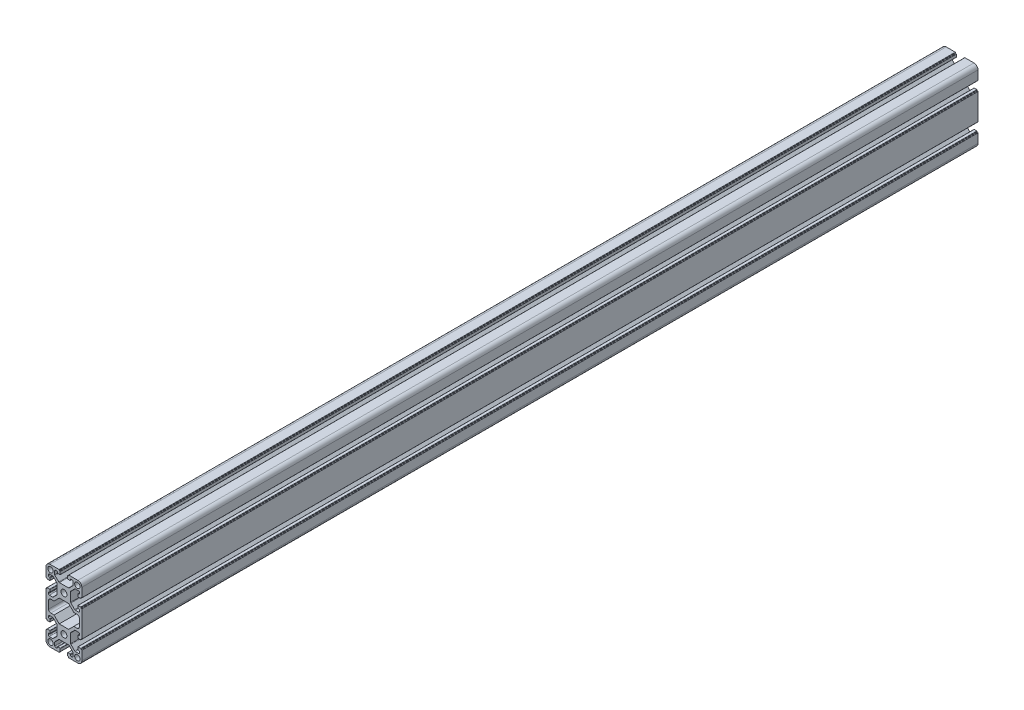
SolidWorks part; units mm, degrees
material "6063 T5"
ref_plane "Спереди" through (0, 0, 0) normal (0, 0, 1) x (1, 0, 0)
ref_plane "Сверху" through (0, 0, 0) normal (0, 1, 0) x (1, 0, 0)
ref_plane "Справа" through (0, 0, 0) normal (1, 0, 0) x (0, 0, -1)
sketch "Эскиз1" plane through (0, 0, 0) normal (0, 0, 1) x (1, 0, 0)
  line L0 (-19.98, 20.5457) -> (20.02, 20.5457) construction
  line L1 (-20, 10.25) -> (-20, 15.5)
  line L2 (-15.5, 20) -> (-10.25, 20)
  line L3 (10.25, 20) -> (15.5, 20)
  line L8 (20, 15.5) -> (20, 10.25)
  line L13 (0, 0) -> (0, -40) construction
  line L14 (0, -20) -> (-27.0056, -20) construction
  line L19 (20, -55.5) -> (20, -50.25)
  line L20 (10.25, -60) -> (15.5, -60)
  line L25 (-15.5, -60) -> (-10.25, -60)
  line L26 (-20.0124, 26.0326) -> (19.9876, 26.0326) construction
  line L27 (-20, -50.25) -> (-20, -55.5)
  line L28 (-20, -10.25) -> (-20, -29.75)
  line L29 (20, -10.25) -> (20, -29.75)
  line L30 (-17.2, -24.25) -> (-17.2, -15.75)
  line L31 (-14.7, -13.25) -> (-11.0074, -13.25)
  line L32 (-11.0074, -13.25) -> (-5.2574, -7.5)
  line L33 (-5.2574, -7.5) -> (5.2574, -7.5)
  line L34 (-29.9759, 20.027) -> (-29.9759, -59.973) construction
  line L35 (11.0074, -13.25) -> (5.2574, -7.5)
  line L36 (14.7, -13.25) -> (11.0074, -13.25)
  line L37 (17.2, -24.25) -> (17.2, -15.75)
  line L38 (-14.7, -26.75) -> (-11.0074, -26.75)
  line L39 (-11.0074, -26.75) -> (-5.2574, -32.5)
  line L40 (-5.2574, -32.5) -> (5.2574, -32.5)
  line L41 (11.0074, -26.75) -> (5.2574, -32.5)
  line L42 (14.7, -26.75) -> (11.0074, -26.75)
  line L45 (20, -10.25) -> (20, -15.5) [skipped]
  line L46 (15.5, -20) -> (10.25, -20) [skipped]
  line L47 (-10.25, -20) -> (-15.5, -20) [skipped]
  line L48 (-20, -15.5) -> (-20, -10.25) [skipped]
  arc A0 (-20, 15.5) -> (-15.5, 20) centre (-15.5, 15.5) cw
  circle A5 centre (0, 0) radius 3.35
  arc A6 (15.5, 20) -> (20, 15.5) centre (15.5, 15.5) cw
  circle A11 centre (15, 15) radius 3
  circle A16 centre (-15, -55) radius 3
  circle A21 centre (15, -55) radius 3
  arc A22 (15.5, -60) -> (20, -55.5) centre (15.5, -55.5) ccw
  circle A23 centre (0, -40) radius 3.35
  arc A24 (-20, -55.5) -> (-15.5, -60) centre (-15.5, -55.5) ccw
  arc A25 (-17.2, -15.75) -> (-14.7, -13.25) centre (-14.7, -15.75) cw
  arc A26 (17.2, -15.75) -> (14.7, -13.25) centre (14.7, -15.75) ccw
  arc A27 (-17.2, -24.25) -> (-14.7, -26.75) centre (-14.7, -24.25) ccw
  arc A28 (17.2, -24.25) -> (14.7, -26.75) centre (14.7, -24.25) cw
  circle A33 centre (-15, 15) radius 3
  arc A37 (20, -15.5) -> (15.5, -20) centre (15.5, -15.5) cw [skipped]
  circle A38 centre (15, -15) radius 3 [skipped]
  arc A39 (-15.5, -20) -> (-20, -15.5) centre (-15.5, -15.5) cw [skipped]
  circle A40 centre (-15, -15) radius 3 [skipped]
  point P5 (0, 0)
  point P35 (0, -40)
  point P36 (0, -40)
  point P38 (0, 0)
  point P63 (0, -7.5)
  point P71 (-17.2, -20)
  point P75 (17.2, -20)
  line B0 (-20, 10.25) -> (-20, 5.4)
  line B1 (-19.7, 5.1) -> (-19.3, 5.1)
  line B2 (-19, 4.8) -> (-19, 4.4)
  line B3 (-18.7, 4.1) -> (-15.8, 4.1)
  line B4 (-15.5, 4.4) -> (-15.5, 6.8)
  line B5 (-15.8, 7.1) -> (-16.3, 7.1)
  line B6 (-17.3, 8.1) -> (-17.3, 9.25)
  line B7 (-16.3, 10.25) -> (-12.6642, 10.25)
  line B8 (-11.9571, 9.9571) -> (-7.7929, 5.7929)
  line B9 (-7.5, 5.0858) -> (-7.5, -5.0858)
  line B10 (-7.5, 0) -> (-20, 0) construction
  line B11 (-11.9571, -9.9571) -> (-7.7929, -5.7929)
  line B12 (-16.3, -10.25) -> (-12.6642, -10.25)
  line B13 (-17.3, -8.1) -> (-17.3, -9.25)
  line B14 (-15.8, -7.1) -> (-16.3, -7.1)
  line B15 (-15.5, -4.4) -> (-15.5, -6.8)
  line B16 (-18.7, -4.1) -> (-15.8, -4.1)
  line B17 (-19, -4.8) -> (-19, -4.4)
  line B18 (-19.7, -5.1) -> (-19.3, -5.1)
  line B19 (-20, -10.25) -> (-20, -5.4)
  arc B20 (-15.5, 6.8) -> (-15.8, 7.1) centre (-15.8, 6.8) ccw
  arc B21 (-15.8, 4.1) -> (-15.5, 4.4) centre (-15.8, 4.4) ccw
  arc B22 (-19, 4.4) -> (-18.7, 4.1) centre (-18.7, 4.4) ccw
  arc B23 (-19.3, 5.1) -> (-19, 4.8) centre (-19.3, 4.8) cw
  arc B24 (-20, 5.4) -> (-19.7, 5.1) centre (-19.7, 5.4) ccw
  arc B25 (-7.7929, 5.7929) -> (-7.5, 5.0858) centre (-8.5, 5.0858) cw
  arc B26 (-12.6642, 10.25) -> (-11.9571, 9.9571) centre (-12.6642, 9.25) cw
  arc B27 (-17.3, 9.25) -> (-16.3, 10.25) centre (-16.3, 9.25) cw
  arc B28 (-16.3, 7.1) -> (-17.3, 8.1) centre (-16.3, 8.1) cw
  arc B29 (-16.3, -7.1) -> (-17.3, -8.1) centre (-16.3, -8.1) ccw
  arc B30 (-17.3, -9.25) -> (-16.3, -10.25) centre (-16.3, -9.25) ccw
  arc B31 (-12.6642, -10.25) -> (-11.9571, -9.9571) centre (-12.6642, -9.25) ccw
  arc B32 (-7.7929, -5.7929) -> (-7.5, -5.0858) centre (-8.5, -5.0858) ccw
  arc B33 (-20, -5.4) -> (-19.7, -5.1) centre (-19.7, -5.4) cw
  arc B34 (-19.3, -5.1) -> (-19, -4.8) centre (-19.3, -4.8) ccw
  arc B35 (-19, -4.4) -> (-18.7, -4.1) centre (-18.7, -4.4) cw
  arc B36 (-15.8, -4.1) -> (-15.5, -4.4) centre (-15.8, -4.4) cw
  arc B37 (-15.5, -6.8) -> (-15.8, -7.1) centre (-15.8, -6.8) cw
  line B38 (10.25, 20) -> (5.4, 20)
  line B39 (5.1, 19.7) -> (5.1, 19.3)
  line B40 (4.8, 19) -> (4.4, 19)
  line B41 (4.1, 18.7) -> (4.1, 15.8)
  line B42 (4.4, 15.5) -> (6.8, 15.5)
  line B43 (7.1, 15.8) -> (7.1, 16.3)
  line B44 (8.1, 17.3) -> (9.25, 17.3)
  line B45 (10.25, 16.3) -> (10.25, 12.6642)
  line B46 (9.9571, 11.9571) -> (5.7929, 7.7929)
  line B47 (5.0858, 7.5) -> (-5.0858, 7.5)
  line B48 (0, 7.5) -> (0, 20) construction
  line B49 (-9.9571, 11.9571) -> (-5.7929, 7.7929)
  line B50 (-10.25, 16.3) -> (-10.25, 12.6642)
  line B51 (-8.1, 17.3) -> (-9.25, 17.3)
  line B52 (-7.1, 15.8) -> (-7.1, 16.3)
  line B53 (-4.4, 15.5) -> (-6.8, 15.5)
  line B54 (-4.1, 18.7) -> (-4.1, 15.8)
  line B55 (-4.8, 19) -> (-4.4, 19)
  line B56 (-5.1, 19.7) -> (-5.1, 19.3)
  line B57 (-10.25, 20) -> (-5.4, 20)
  arc B58 (6.8, 15.5) -> (7.1, 15.8) centre (6.8, 15.8) ccw
  arc B59 (4.1, 15.8) -> (4.4, 15.5) centre (4.4, 15.8) ccw
  arc B60 (4.4, 19) -> (4.1, 18.7) centre (4.4, 18.7) ccw
  arc B61 (5.1, 19.3) -> (4.8, 19) centre (4.8, 19.3) cw
  arc B62 (5.4, 20) -> (5.1, 19.7) centre (5.4, 19.7) ccw
  arc B63 (5.7929, 7.7929) -> (5.0858, 7.5) centre (5.0858, 8.5) cw
  arc B64 (10.25, 12.6642) -> (9.9571, 11.9571) centre (9.25, 12.6642) cw
  arc B65 (9.25, 17.3) -> (10.25, 16.3) centre (9.25, 16.3) cw
  arc B66 (7.1, 16.3) -> (8.1, 17.3) centre (8.1, 16.3) cw
  arc B67 (-7.1, 16.3) -> (-8.1, 17.3) centre (-8.1, 16.3) ccw
  arc B68 (-9.25, 17.3) -> (-10.25, 16.3) centre (-9.25, 16.3) ccw
  arc B69 (-10.25, 12.6642) -> (-9.9571, 11.9571) centre (-9.25, 12.6642) ccw
  arc B70 (-5.7929, 7.7929) -> (-5.0858, 7.5) centre (-5.0858, 8.5) ccw
  arc B71 (-5.4, 20) -> (-5.1, 19.7) centre (-5.4, 19.7) cw
  arc B72 (-5.1, 19.3) -> (-4.8, 19) centre (-4.8, 19.3) ccw
  arc B73 (-4.4, 19) -> (-4.1, 18.7) centre (-4.4, 18.7) cw
  arc B74 (-4.1, 15.8) -> (-4.4, 15.5) centre (-4.4, 15.8) cw
  arc B75 (-6.8, 15.5) -> (-7.1, 15.8) centre (-6.8, 15.8) cw
  line B76 (20, -10.25) -> (20, -5.4)
  line B77 (19.7, -5.1) -> (19.3, -5.1)
  line B78 (19, -4.8) -> (19, -4.4)
  line B79 (18.7, -4.1) -> (15.8, -4.1)
  line B80 (15.5, -4.4) -> (15.5, -6.8)
  line B81 (15.8, -7.1) -> (16.3, -7.1)
  line B82 (17.3, -8.1) -> (17.3, -9.25)
  line B83 (16.3, -10.25) -> (12.6642, -10.25)
  line B84 (11.9571, -9.9571) -> (7.7929, -5.7929)
  line B85 (7.5, -5.0858) -> (7.5, 5.0858)
  line B86 (7.5, 0) -> (20, 0) construction
  line B87 (11.9571, 9.9571) -> (7.7929, 5.7929)
  line B88 (16.3, 10.25) -> (12.6642, 10.25)
  line B89 (17.3, 8.1) -> (17.3, 9.25)
  line B90 (15.8, 7.1) -> (16.3, 7.1)
  line B91 (15.5, 4.4) -> (15.5, 6.8)
  line B92 (18.7, 4.1) -> (15.8, 4.1)
  line B93 (19, 4.8) -> (19, 4.4)
  line B94 (19.7, 5.1) -> (19.3, 5.1)
  line B95 (20, 10.25) -> (20, 5.4)
  arc B96 (15.5, -6.8) -> (15.8, -7.1) centre (15.8, -6.8) ccw
  arc B97 (15.8, -4.1) -> (15.5, -4.4) centre (15.8, -4.4) ccw
  arc B98 (19, -4.4) -> (18.7, -4.1) centre (18.7, -4.4) ccw
  arc B99 (19.3, -5.1) -> (19, -4.8) centre (19.3, -4.8) cw
  arc B100 (20, -5.4) -> (19.7, -5.1) centre (19.7, -5.4) ccw
  arc B101 (7.7929, -5.7929) -> (7.5, -5.0858) centre (8.5, -5.0858) cw
  arc B102 (12.6642, -10.25) -> (11.9571, -9.9571) centre (12.6642, -9.25) cw
  arc B103 (17.3, -9.25) -> (16.3, -10.25) centre (16.3, -9.25) cw
  arc B104 (16.3, -7.1) -> (17.3, -8.1) centre (16.3, -8.1) cw
  arc B105 (16.3, 7.1) -> (17.3, 8.1) centre (16.3, 8.1) ccw
  arc B106 (17.3, 9.25) -> (16.3, 10.25) centre (16.3, 9.25) ccw
  arc B107 (12.6642, 10.25) -> (11.9571, 9.9571) centre (12.6642, 9.25) ccw
  arc B108 (7.7929, 5.7929) -> (7.5, 5.0858) centre (8.5, 5.0858) ccw
  arc B109 (20, 5.4) -> (19.7, 5.1) centre (19.7, 5.4) cw
  arc B110 (19.3, 5.1) -> (19, 4.8) centre (19.3, 4.8) ccw
  arc B111 (19, 4.4) -> (18.7, 4.1) centre (18.7, 4.4) cw
  arc B112 (15.8, 4.1) -> (15.5, 4.4) centre (15.8, 4.4) cw
  arc B113 (15.5, 6.8) -> (15.8, 7.1) centre (15.8, 6.8) cw
  line B114 (10.25, -60) -> (5.4, -60)
  line B115 (5.1, -59.7) -> (5.1, -59.3)
  line B116 (4.8, -59) -> (4.4, -59)
  line B117 (4.1, -58.7) -> (4.1, -55.8)
  line B118 (4.4, -55.5) -> (6.8, -55.5)
  line B119 (7.1, -55.8) -> (7.1, -56.3)
  line B120 (8.1, -57.3) -> (9.25, -57.3)
  line B121 (10.25, -56.3) -> (10.25, -52.6642)
  line B122 (9.9571, -51.9571) -> (5.7929, -47.7929)
  line B123 (5.0858, -47.5) -> (-5.0858, -47.5)
  line B124 (0, -47.5) -> (0, -60) construction
  line B125 (-9.9571, -51.9571) -> (-5.7929, -47.7929)
  line B126 (-10.25, -56.3) -> (-10.25, -52.6642)
  line B127 (-8.1, -57.3) -> (-9.25, -57.3)
  line B128 (-7.1, -55.8) -> (-7.1, -56.3)
  line B129 (-4.4, -55.5) -> (-6.8, -55.5)
  line B130 (-4.1, -58.7) -> (-4.1, -55.8)
  line B131 (-4.8, -59) -> (-4.4, -59)
  line B132 (-5.1, -59.7) -> (-5.1, -59.3)
  line B133 (-10.25, -60) -> (-5.4, -60)
  arc B134 (6.8, -55.5) -> (7.1, -55.8) centre (6.8, -55.8) cw
  arc B135 (4.1, -55.8) -> (4.4, -55.5) centre (4.4, -55.8) cw
  arc B136 (4.4, -59) -> (4.1, -58.7) centre (4.4, -58.7) cw
  arc B137 (5.1, -59.3) -> (4.8, -59) centre (4.8, -59.3) ccw
  arc B138 (5.4, -60) -> (5.1, -59.7) centre (5.4, -59.7) cw
  arc B139 (5.7929, -47.7929) -> (5.0858, -47.5) centre (5.0858, -48.5) ccw
  arc B140 (10.25, -52.6642) -> (9.9571, -51.9571) centre (9.25, -52.6642) ccw
  arc B141 (9.25, -57.3) -> (10.25, -56.3) centre (9.25, -56.3) ccw
  arc B142 (7.1, -56.3) -> (8.1, -57.3) centre (8.1, -56.3) ccw
  arc B143 (-7.1, -56.3) -> (-8.1, -57.3) centre (-8.1, -56.3) cw
  arc B144 (-9.25, -57.3) -> (-10.25, -56.3) centre (-9.25, -56.3) cw
  arc B145 (-10.25, -52.6642) -> (-9.9571, -51.9571) centre (-9.25, -52.6642) cw
  arc B146 (-5.7929, -47.7929) -> (-5.0858, -47.5) centre (-5.0858, -48.5) cw
  arc B147 (-5.4, -60) -> (-5.1, -59.7) centre (-5.4, -59.7) ccw
  arc B148 (-5.1, -59.3) -> (-4.8, -59) centre (-4.8, -59.3) cw
  arc B149 (-4.4, -59) -> (-4.1, -58.7) centre (-4.4, -58.7) ccw
  arc B150 (-4.1, -55.8) -> (-4.4, -55.5) centre (-4.4, -55.8) ccw
  arc B151 (-6.8, -55.5) -> (-7.1, -55.8) centre (-6.8, -55.8) ccw
  line B152 (-20, -50.25) -> (-20, -45.4)
  line B153 (-19.7, -45.1) -> (-19.3, -45.1)
  line B154 (-19, -44.8) -> (-19, -44.4)
  line B155 (-18.7, -44.1) -> (-15.8, -44.1)
  line B156 (-15.5, -44.4) -> (-15.5, -46.8)
  line B157 (-15.8, -47.1) -> (-16.3, -47.1)
  line B158 (-17.3, -48.1) -> (-17.3, -49.25)
  line B159 (-16.3, -50.25) -> (-12.6642, -50.25)
  line B160 (-11.9571, -49.9571) -> (-7.7929, -45.7929)
  line B161 (-7.5, -45.0858) -> (-7.5, -34.9142)
  line B162 (-7.5, -40) -> (-20, -40) construction
  line B163 (-11.9571, -30.0429) -> (-7.7929, -34.2071)
  line B164 (-16.3, -29.75) -> (-12.6642, -29.75)
  line B165 (-17.3, -31.9) -> (-17.3, -30.75)
  line B166 (-15.8, -32.9) -> (-16.3, -32.9)
  line B167 (-15.5, -35.6) -> (-15.5, -33.2)
  line B168 (-18.7, -35.9) -> (-15.8, -35.9)
  line B169 (-19, -35.2) -> (-19, -35.6)
  line B170 (-19.7, -34.9) -> (-19.3, -34.9)
  line B171 (-20, -29.75) -> (-20, -34.6)
  arc B172 (-15.5, -46.8) -> (-15.8, -47.1) centre (-15.8, -46.8) cw
  arc B173 (-15.8, -44.1) -> (-15.5, -44.4) centre (-15.8, -44.4) cw
  arc B174 (-19, -44.4) -> (-18.7, -44.1) centre (-18.7, -44.4) cw
  arc B175 (-19.3, -45.1) -> (-19, -44.8) centre (-19.3, -44.8) ccw
  arc B176 (-20, -45.4) -> (-19.7, -45.1) centre (-19.7, -45.4) cw
  arc B177 (-7.7929, -45.7929) -> (-7.5, -45.0858) centre (-8.5, -45.0858) ccw
  arc B178 (-12.6642, -50.25) -> (-11.9571, -49.9571) centre (-12.6642, -49.25) ccw
  arc B179 (-17.3, -49.25) -> (-16.3, -50.25) centre (-16.3, -49.25) ccw
  arc B180 (-16.3, -47.1) -> (-17.3, -48.1) centre (-16.3, -48.1) ccw
  arc B181 (-16.3, -32.9) -> (-17.3, -31.9) centre (-16.3, -31.9) cw
  arc B182 (-17.3, -30.75) -> (-16.3, -29.75) centre (-16.3, -30.75) cw
  arc B183 (-12.6642, -29.75) -> (-11.9571, -30.0429) centre (-12.6642, -30.75) cw
  arc B184 (-7.7929, -34.2071) -> (-7.5, -34.9142) centre (-8.5, -34.9142) cw
  arc B185 (-20, -34.6) -> (-19.7, -34.9) centre (-19.7, -34.6) ccw
  arc B186 (-19.3, -34.9) -> (-19, -35.2) centre (-19.3, -35.2) cw
  arc B187 (-19, -35.6) -> (-18.7, -35.9) centre (-18.7, -35.6) ccw
  arc B188 (-15.8, -35.9) -> (-15.5, -35.6) centre (-15.8, -35.6) ccw
  arc B189 (-15.5, -33.2) -> (-15.8, -32.9) centre (-15.8, -33.2) ccw
  line B190 (20, -29.75) -> (20, -34.6)
  line B191 (19.7, -34.9) -> (19.3, -34.9)
  line B192 (19, -35.2) -> (19, -35.6)
  line B193 (18.7, -35.9) -> (15.8, -35.9)
  line B194 (15.5, -35.6) -> (15.5, -33.2)
  line B195 (15.8, -32.9) -> (16.3, -32.9)
  line B196 (17.3, -31.9) -> (17.3, -30.75)
  line B197 (16.3, -29.75) -> (12.6642, -29.75)
  line B198 (11.9571, -30.0429) -> (7.7929, -34.2071)
  line B199 (7.5, -34.9142) -> (7.5, -45.0858)
  line B200 (7.5, -40) -> (20, -40) construction
  line B201 (11.9571, -49.9571) -> (7.7929, -45.7929)
  line B202 (16.3, -50.25) -> (12.6642, -50.25)
  line B203 (17.3, -48.1) -> (17.3, -49.25)
  line B204 (15.8, -47.1) -> (16.3, -47.1)
  line B205 (15.5, -44.4) -> (15.5, -46.8)
  line B206 (18.7, -44.1) -> (15.8, -44.1)
  line B207 (19, -44.8) -> (19, -44.4)
  line B208 (19.7, -45.1) -> (19.3, -45.1)
  line B209 (20, -50.25) -> (20, -45.4)
  arc B210 (15.5, -33.2) -> (15.8, -32.9) centre (15.8, -33.2) cw
  arc B211 (15.8, -35.9) -> (15.5, -35.6) centre (15.8, -35.6) cw
  arc B212 (19, -35.6) -> (18.7, -35.9) centre (18.7, -35.6) cw
  arc B213 (19.3, -34.9) -> (19, -35.2) centre (19.3, -35.2) ccw
  arc B214 (20, -34.6) -> (19.7, -34.9) centre (19.7, -34.6) cw
  arc B215 (7.7929, -34.2071) -> (7.5, -34.9142) centre (8.5, -34.9142) ccw
  arc B216 (12.6642, -29.75) -> (11.9571, -30.0429) centre (12.6642, -30.75) ccw
  arc B217 (17.3, -30.75) -> (16.3, -29.75) centre (16.3, -30.75) ccw
  arc B218 (16.3, -32.9) -> (17.3, -31.9) centre (16.3, -31.9) ccw
  arc B219 (16.3, -47.1) -> (17.3, -48.1) centre (16.3, -48.1) cw
  arc B220 (17.3, -49.25) -> (16.3, -50.25) centre (16.3, -49.25) cw
  arc B221 (12.6642, -50.25) -> (11.9571, -49.9571) centre (12.6642, -49.25) cw
  arc B222 (7.7929, -45.7929) -> (7.5, -45.0858) centre (8.5, -45.0858) cw
  arc B223 (20, -45.4) -> (19.7, -45.1) centre (19.7, -45.4) ccw
  arc B224 (19.3, -45.1) -> (19, -44.8) centre (19.3, -44.8) cw
  arc B225 (19, -44.4) -> (18.7, -44.1) centre (18.7, -44.4) ccw
  arc B226 (15.8, -44.1) -> (15.5, -44.4) centre (15.8, -44.4) ccw
  arc B227 (15.5, -46.8) -> (15.8, -47.1) centre (15.8, -46.8) ccw
  dimension "D12" = 3
  dimension "D13" = 3
  dimension "D2" = 4.5
  dimension "D3" = 6
  dimension "D5" = 15
  dimension "D6" = 6.7
  dimension "D4" = 15
  dimension "D15" = 2.5
  dimension "D1" = 20
  dimension "D7" = 40
  dimension "D8" = 4
  dimension "D9" = 40
  dimension "D10" = 80
  dimension "D11" = 7.5
  dimension "D14" = 2.8
sketch_block_instance "8B(20,5PL)-1"
sketch_block "8B(20,5PL)" parameters "D7"=0.3, "D8"=1, "D1"=12.5, "D2"=4.5, "D3"=8.2, "D4"=20.5, "D5"=10.2, "D6"=135, "D9"=11.8, "D10"=4.85, "D11"=1.65, "D12"=0.6
sketch_block_instance "8B(20,5PL)-3"
sketch_block_instance "8B(20,5PL)-4"
sketch_block_instance "8B(20,5PL)-6"
sketch_block_instance "8B(20,5PL)-7"
sketch_block_instance "8B(20,5PL)-8"
sketch_block_instance "8B(20,5PL)-9"
extrude "Бобышка-Вытянуть1" add sketch "Эскиз1" along normal blind 1000
